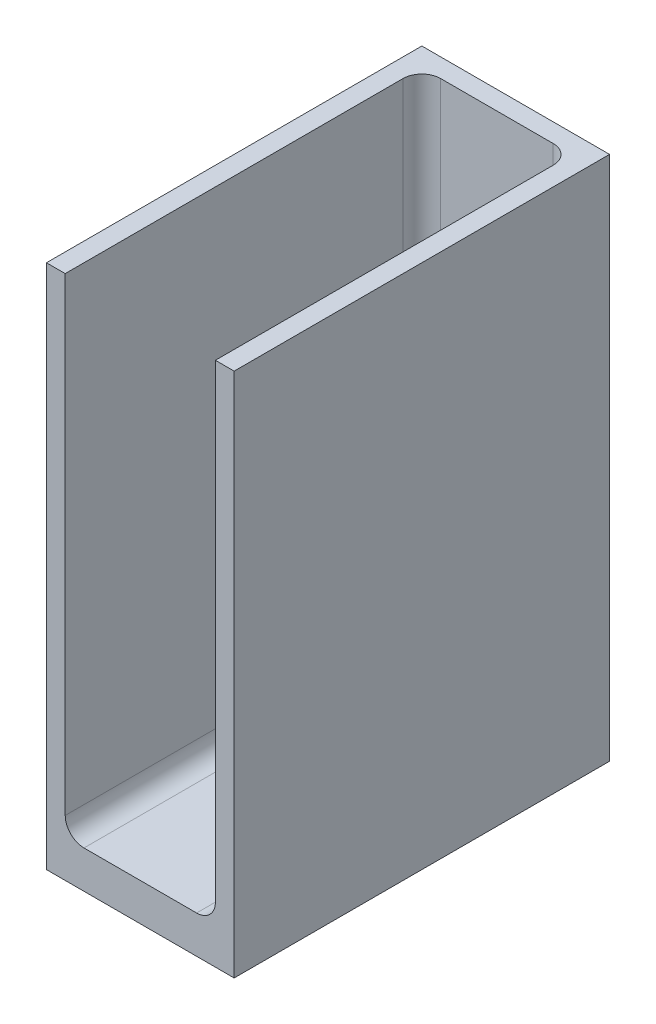
SolidWorks part; units mm, degrees
ref_plane "Front Plane" through (0, 0, 0) normal (0, 0, 1) x (1, 0, 0)
ref_plane "Top Plane" through (0, 0, 0) normal (0, 1, 0) x (1, 0, 0)
ref_plane "Right Plane" through (0, 0, 0) normal (1, 0, 0) x (0, 0, -1)
sketch "Sketch1" plane through (0, 0, 0) normal (0, 1, 0) x (1, 0, 0)
  line L1 (-12.7, -25.4) -> (12.7, -25.4)
  line L2 (-12.7, -25.4) -> (-12.7, 25.4)
  line L3 (-12.7, 25.4) -> (12.7, 25.4)
  line L4 (12.7, -25.4) -> (12.7, 25.4)
  line L5 (-12.7, -25.4) -> (12.7, 25.4) construction
  line L6 (-12.7, 25.4) -> (12.7, -25.4) construction
  point P0 (0, 0)
  dimension "D1" = 50.8
  dimension "D2" = 25.4
extrude "Boss-Extrude1" add sketch "Sketch1" along normal blind 5.08
sketch "Sketch2" plane through (0, 5.08, 0) normal (0, 1, 0) x (1, 0, 0)
  line L0 (-12.7, -25.4) -> (-12.7, 25.4)
  line L1 (-12.7, 25.4) -> (12.7, 25.4)
  line L2 (12.7, 25.4) -> (12.7, -25.4)
  line L3 (12.7, -25.4) -> (10.16, -25.4)
  line L4 (-12.7, -25.4) -> (12.7, -25.4) construction
  line L5 (10.16, -25.4) -> (10.16, 22.86)
  line L6 (10.16, 22.86) -> (-10.16, 22.86)
  line L7 (-10.16, 22.86) -> (-10.16, -25.4)
  line L8 (-10.16, -25.4) -> (-12.7, -25.4)
  dimension "D1" = 2.54
  dimension "D2" = 2.54
  dimension "D3" = 2.54
extrude "Boss-Extrude2" add sketch "Sketch2" along normal blind 66.04
fillet "Fillet1" radius 2.54 5 edges at (-10.16, 38.1, -22.86) (10.16, 5.08, 1.27) (-10.16, 5.08, 1.27) (0, 5.08, -22.86) (10.16, 38.1, -22.86)
